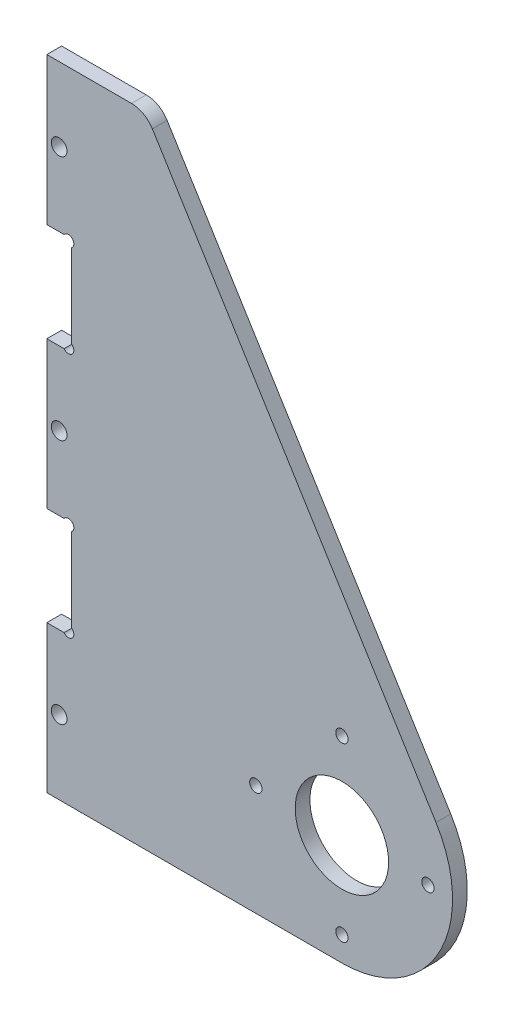
SolidWorks part; units mm, degrees
material "3.1325 (EN-AW 2017A)"
ref_plane "正面" through (0, 0, 0) normal (0, 0, 1) x (1, 0, 0)
ref_plane "平面" through (0, 0, 0) normal (0, 1, 0) x (1, 0, 0)
ref_plane "右側面" through (0, 0, 0) normal (1, 0, 0) x (0, 0, -1)
sketch "ｽｹｯﾁ2" plane through (0, 0, 0) normal (0, 0, 1) x (1, 0, 0)
  line L0 (17.5, 0) -> (-17.5, 0) construction
  line L1 (0, -17.5) -> (0, 17.5) construction
  line L5 (-60, 107.5) -> (-60, -22.5)
  line L6 (-60, -22.5) -> (-40, -22.5)
  line L7 (-60, 107.5) -> (-40, 107.5)
  line L8 (-40, 107.5) -> (-40, -22.5) construction
  line L9 (-40, 107.5) -> (19.1386, 11.8306)
  line L10 (-40, -22.5) -> (0, -22.5)
  line L14 (0, -50) -> (-60, -50) construction
  line L15 (-60, -22.5) -> (-60, -50) construction
  line L17 (-40, -22.5015) -> (-40, -22.5) construction
  circle A0 centre (0, 0) radius 9.5
  circle A1 centre (0, 17.5) radius 1.25
  circle A2 centre (17.5, 0) radius 1.25
  circle A3 centre (0, -17.5) radius 1.25
  circle A4 centre (-17.5, 0) radius 1.25
  arc A8 (0, -22.5) -> (19.1386, 11.8306) centre (0, 0) ccw
  circle A9 centre (0, 0) radius 50 construction
  point P6 (0, 0)
  point P9 (0, 0)
  dimension "D1" = 19
  dimension "D2" = 2.5
  dimension "D3" = 130
  dimension "D8" = 22.5
  dimension "D9" = 20
  dimension "D12" = 100
  dimension "D13" = 60
  dimension "D7" = 35
extrude "ﾎﾞｽ - 押し出し1" add sketch "ｽｹｯﾁ2" along normal blind 3
fillet "ﾌｨﾚｯﾄ3" radius 5 1 edges at (-40, 107.5, 1.5)
sketch "ｽｹｯﾁ4" plane through (0, 0, 3) normal (0, 0, 1) x (1, 0, 0)
  line L0 (-60, 107.5) -> (-60, -22.5) construction
  line L1 (-60, 77.55) -> (-54.95, 77.55)
  line L2 (-60, 77.55) -> (-60, 57.45)
  line L3 (-60, 57.45) -> (-54.95, 57.45)
  line L4 (-54.95, 77.55) -> (-54.95, 57.45)
  line L5 (-60, -22.5) -> (0, -22.5) construction
  line L6 (-60, 27.55) -> (-54.95, 27.55)
  line L7 (-60, 27.55) -> (-60, 7.45)
  line L8 (-60, 7.45) -> (-54.95, 7.45)
  line L9 (-54.95, 27.55) -> (-54.95, 7.45)
  line L10 (-42.7874, 107.5) -> (-60, 107.5) construction
  circle A0 centre (-57.5, -7.5) radius 1.6
  circle A1 centre (-57.5, 42.5) radius 1.6
  circle A2 centre (-57.5, 92.5) radius 1.6
  circle A3 centre (-55.61, 26.89) radius 1.1
  circle A4 centre (-55.61, 8.11) radius 1.1
  circle A5 centre (-55.61, 58.11) radius 1.1
  circle A6 centre (-55.61, 76.89) radius 1.1
  line M13 (-60, 107.5) -> (-60, -22.5)
  dimension "D7" = 3.2
  dimension "D8" = 2.5
  dimension "D9" = 15
  dimension "D11" = 15
  dimension "D12" = 2.2
  dimension "D13" = 2.2
  dimension "D14" = 0.66
  dimension "D15" = 0.66
  dimension "D17" = 0.66
  dimension "D18" = 0.66
  dimension "D19" = 0.66
  dimension "0" = 29.95
  dimension "D2" = 29.9
  dimension "D3" = 29.95
  dimension "D4" = 20.1
  dimension "D5" = 5.05
  dimension "D6" = 5.05
  dimension "D16" = 2
  dimension "D10" = 3
extrude "ｶｯﾄ - 押し出し1" cut sketch "ｽｹｯﾁ4" against normal blind 10 contours A2 | A6 L1 L3 A5 L4 M13 | A1 | A3 | L8 L7 L6 L9 | A0 | A4
